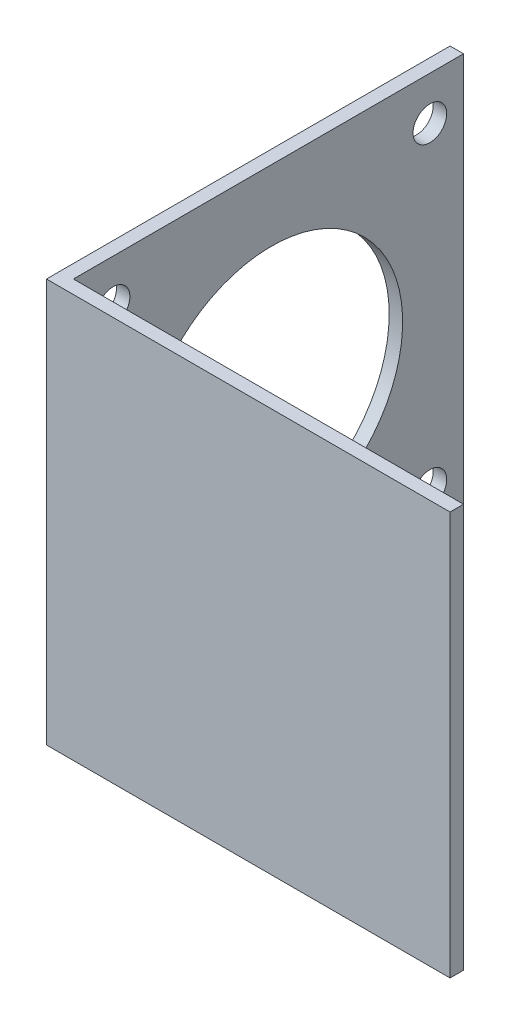
SolidWorks part; units mm, degrees
ref_plane "Front Plane" through (0, 0, 0) normal (0, 0, 1) x (1, 0, 0)
ref_plane "Top Plane" through (0, 0, 0) normal (0, 1, 0) x (1, 0, 0)
ref_plane "Right Plane" through (0, 0, 0) normal (1, 0, 0) x (0, 0, -1)
sketch "Sketch1" plane through (0, 0, 0) normal (0, 1, 0) x (1, 0, 0)
  line L0 (0, 60) -> (0, 0)
  line L1 (0, 0) -> (60, 0)
  line L2 (2, 60) -> (2, 2)
  line L3 (2, 2) -> (60, 2)
  line L4 (0, 60) -> (2, 60)
  line L5 (60, 2) -> (60, 0)
  dimension "D2" = 60
  dimension "D3" = 60
  dimension "D1" = 2
extrude "Boss-Extrude1" add sketch "Sketch1" along normal blind 60
sketch "Sketch2" plane through (0, 0, 0) normal (-1, 0, 0) x (0, 0, 1)
  line L0 (-60, 30) -> (0, 30) construction
  line L1 (-60, 60) -> (-60, 0) construction
  line L2 (0, 60) -> (0, 0) construction
  line L4 (-55, 53.55) -> (-7.9, 53.55) construction
  line L5 (-55, 53.55) -> (-55, 6.45) construction
  line L6 (-55, 6.45) -> (-7.9, 6.45) construction
  line L7 (-7.9, 53.55) -> (-7.9, 6.45) construction
  line L8 (-55, 53.55) -> (-7.9, 6.45) construction
  line L9 (-55, 6.45) -> (-7.9, 53.55) construction
  circle A0 centre (-55, 53.55) radius 2.5
  circle A1 centre (-7.9, 53.55) radius 2.5
  circle A2 centre (-7.9, 6.45) radius 2.5
  circle A3 centre (-55, 6.45) radius 2.5
  circle A4 centre (-31.45, 30) radius 19.5
  point P6 (-31.45, 30)
  point P21 (-31.45, 30)
  dimension "D4" = 5
  dimension "D6" = 39
  dimension "D1" = 5
  dimension "D2" = 47.1
  dimension "D3" = 47.1
  dimension "D5" = 4
extrude "Cut-Extrude1" cut sketch "Sketch2" against normal through all both and the other way through all
